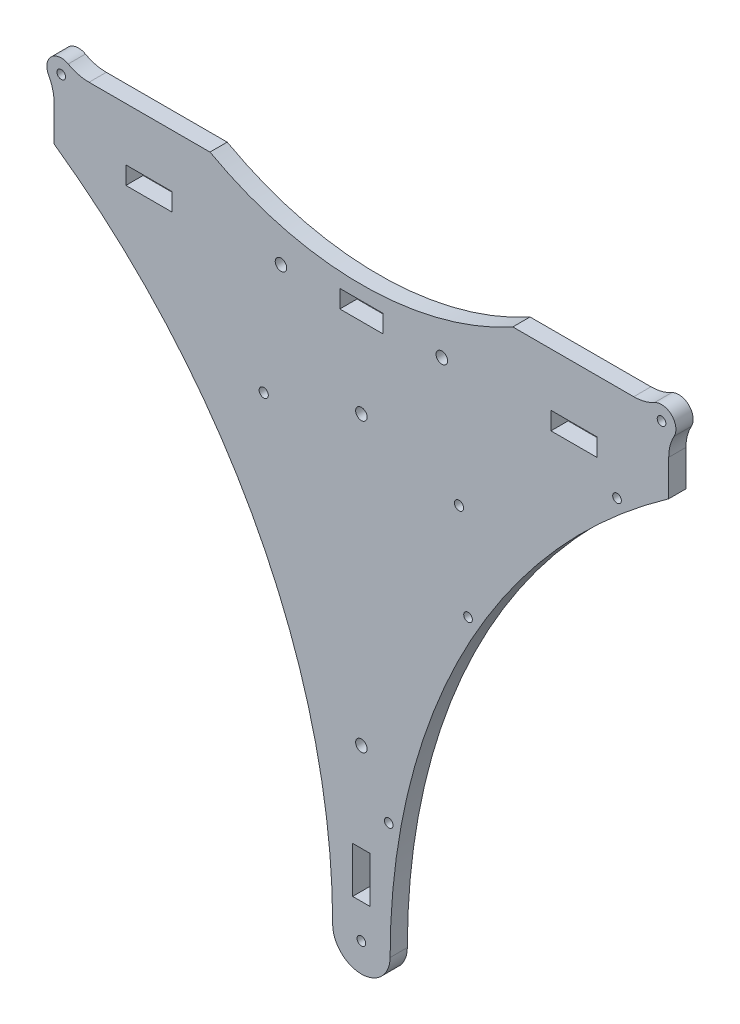
SolidWorks part; units mm, degrees
material "Oak"
ref_plane "Front Plane" through (0, 0, 0) normal (0, 0, 1) x (1, 0, 0)
ref_plane "Top Plane" through (0, 0, 0) normal (0, 1, 0) x (1, 0, 0)
ref_plane "Right Plane" through (0, 0, 0) normal (1, 0, 0) x (0, 0, -1)
sketch "Sketch1" plane through (0, 0, 0) normal (0, 0, 1) x (1, 0, 0)
  line L0 (-66, 82.3) -> (66, 82.3) construction
  line L1 (0, 82.3) -> (0, 0) construction
  line L2 (86.2011, 107) -> (94.8175, 107)
  line L6 (0, -76.6) -> (0, -116.5) construction
  line L7 (-10, -104.5) -> (10, -104.5) construction
  line L8 (-107, 82.3) -> (-107, 94.8175)
  line L9 (-94.8175, 107) -> (-91.7989, 107)
  line L10 (107, 82.3) -> (107, 94.8175)
  line L13 (-82, 88.5) -> (-66, 88.5)
  line L14 (-82, 88.5) -> (-82, 82.3)
  line L15 (-82, 82.3) -> (-66, 82.3)
  line L16 (-66, 88.5) -> (-66, 82.3)
  line L17 (82, 88.5) -> (66, 88.5)
  line L18 (82, 88.5) -> (82, 82.3)
  line L19 (82, 82.3) -> (66, 82.3)
  line L20 (66, 88.5) -> (66, 82.3)
  line L21 (-3.05, -92.6) -> (3.05, -92.6)
  line L22 (-3.05, -92.6) -> (-3.05, -76.6)
  line L23 (-3.05, -76.6) -> (3.05, -76.6)
  line L24 (3.05, -92.6) -> (3.05, -76.6)
  line L32 (52.7171, 107) -> (86.2011, 107)
  line L33 (-7.5, 82.3) -> (7.5, 82.3)
  line L34 (-7.5, 82.3) -> (-7.5, 88.5)
  line L35 (-7.5, 88.5) -> (7.5, 88.5)
  line L36 (7.5, 82.3) -> (7.5, 88.5)
  line L37 (-28, 85.4) -> (28, 85.4) construction
  line L38 (0, 82.3) -> (0, 88.5) construction
  line L40 (-91.7989, 107) -> (-52.7171, 107)
  circle A0 centre (-104.5, 104.5) radius 1.5
  circle A1 centre (104.5, 104.5) radius 1.5
  arc A2 (-52.7171, 107) -> (52.7171, 107) centre (0, 202.3724) ccw
  circle A3 centre (-28, 85.4) radius 2
  circle A4 centre (0, 104.5) radius 1.5 construction
  circle A5 centre (-34, 43.8) radius 1.6
  circle A6 centre (0, 54.4) radius 2
  circle A7 centre (0, -104.5) radius 1.5
  arc A8 (-10, -104.5) -> (10, -104.5) centre (0, -104.5) ccw
  circle A9 centre (0, -45.6) radius 2
  circle A10 centre (28, 85.4) radius 2
  circle A11 centre (-104.5, 0) radius 1.5 [skipped]
  arc A12 (-10, -104.5) -> (-107, 82.3) centre (-238.3672, -104.5) ccw
  arc A13 (10, -104.5) -> (107, 82.3) centre (238.3672, -104.5) cw
  circle A14 centre (104.5, -104.5) radius 1.5 [skipped]
  circle A15 centre (-104.5, -104.5) radius 1.5 [skipped]
  circle A16 centre (104.5, 0) radius 1.5 [skipped]
  arc A17 (108.875, 102.0794) -> (102.0794, 108.875) centre (104.5, 104.5) ccw
  arc A18 (108.875, 102.0794) -> (107, 94.8175) centre (122, 94.8175) ccw
  arc A19 (102.0794, 108.875) -> (94.8175, 107) centre (94.8175, 122) cw
  arc A20 (-102.0794, 108.875) -> (-108.875, 102.0794) centre (-104.5, 104.5) ccw
  arc A21 (-108.875, 102.0794) -> (-107, 94.8175) centre (-122, 94.8175) cw
  arc A22 (-102.0794, 108.875) -> (-94.8175, 107) centre (-94.8175, 122) ccw
  circle A23 centre (34, 43.8) radius 1.6
  point P36 (0, 93.4)
  point P69 (0, 85.4)
  dimension "D4" = 3
  dimension "D16" = 13.6
  dimension "D23" = 28
  dimension "D10" = 4
  dimension "D11" = 100
  dimension "D19" = 3.2
  dimension "D20" = 15
  dimension "D26" = 5
  dimension "D5" = 209
  dimension "D6" = 6.2
  dimension "D7" = 16
  dimension "D8" = 18.5
  dimension "D9" = 181.1
  dimension "D12" = 20
  dimension "D13" = 4
  dimension "D14" = 31
  dimension "D15" = 214
  dimension "D17" = 82
  dimension "D21" = 15
  dimension "D22" = 6.1
  dimension "D24" = 38.5
  dimension "D25" = 34
extrude "Boss-Extrude1" add sketch "Sketch1" along normal blind 6
sketch "Sketch2" plane through (0, 0, 6) normal (0, 0, 1) x (1, 0, 0)
  line L0 (238.3672, -104.5) -> (0, -104.5) construction
  line L1 (238.3672, -104.5) -> (9.5302, -64.1499) construction
  line L2 (238.3672, -104.5) -> (37.1313, 11.6836) construction
  line L3 (238.3672, -104.5) -> (89.0044, 73.5036) construction
  arc A0 (117.5495, 93.9883) -> (6.5512, -120.4956) centre (238.3672, -104.5) ccw construction
  arc A1 (107, 82.3) -> (10, -104.5) centre (238.3672, -104.5) ccw construction
  circle A2 centre (9.5302, -64.1499) radius 1.5
  circle A3 centre (37.1313, 11.6836) radius 1.5
  circle A4 centre (89.0044, 73.5036) radius 1.5
  dimension "D1" = 4
  dimension "D2" = 3
  dimension "D3" = 10
  dimension "D4" = 30
  dimension "D5" = 50
extrude "Cut-Extrude1" cut sketch "Sketch2" against normal through all
equation "\"bed-plate-thickness\"=6"
equation "\"D1@Boss-Extrude1\"=\"bed-plate-thickness\""
equation "\"D22@Sketch1\"=\"y-cross-rib-thickness\"+0.1"
equation "\"D6@Sketch1\"=\"y-rib-thickness\"+0.2"
equation "\"y-cross-rib-thickness\"=6"
equation "\"y-rib-thickness\"=6"
equation "\"x-plate-thickness\"=5"
equation "\"rod-diameter\"=12"
equation "\"t-nut-hole-diameter\"=3"
equation "\"D14@Sketch1\"=28+(\"y-rib-thickness\"/2)"
